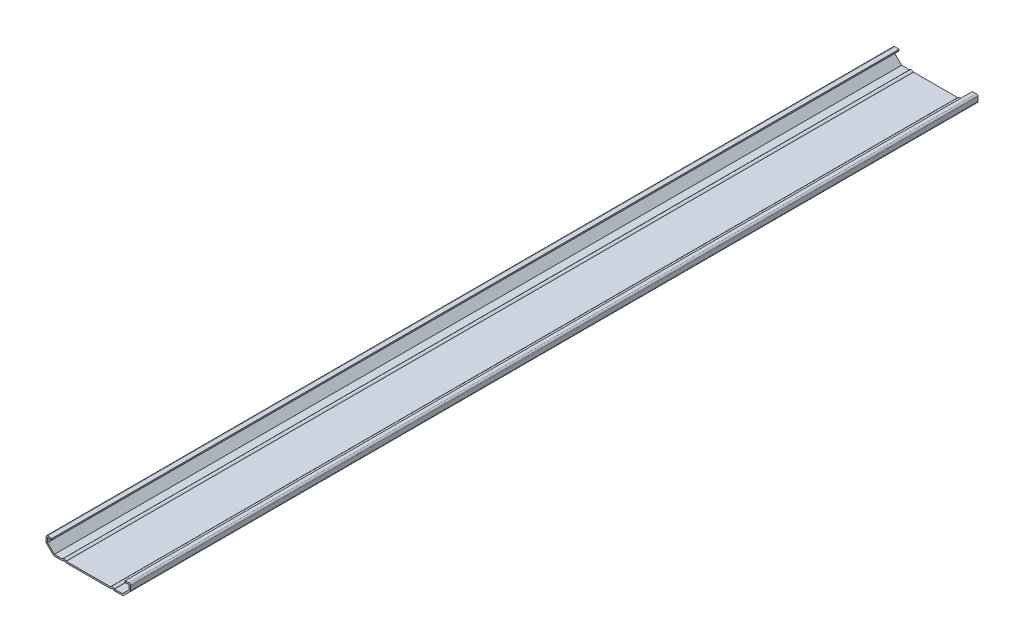
SolidWorks part; units mm, degrees
ref_plane "Front Plane" through (0, 0, 0) normal (0, 0, 1) x (1, 0, 0)
ref_plane "Top Plane" through (0, 0, 0) normal (0, 1, 0) x (1, 0, 0)
ref_plane "Right Plane" through (0, 0, 0) normal (1, 0, 0) x (0, 0, -1)
sketch "Sketch1" plane through (0, 0, 0) normal (0, 0, 1) x (1, 0, 0)
  line L0 (0, 0) -> (0, 6.056) construction
  line L1 (19.05, 0) -> (-19.05, 0)
  line L2 (-20.6375, 0) -> (-28.575, 0)
  line L3 (-28.575, 0) -> (-34.925, 6.35)
  line L4 (-34.925, 6.35) -> (-34.925, 11.9062)
  line L5 (-34.925, 11.9062) -> (-30.1625, 11.5094)
  line L6 (34.925, 11.9062) -> (30.1625, 11.5094)
  line L7 (34.925, 6.35) -> (34.925, 11.9062)
  line L8 (28.575, 0) -> (34.925, 6.35)
  line L9 (20.6375, 0) -> (28.575, 0)
  arc A0 (-19.05, 0) -> (-20.6375, 0) centre (-19.8437, 0) ccw
  arc A1 (19.05, 0) -> (20.6375, 0) centre (19.8437, 0) cw
  point P7 (-15.8425, 0)
  point P11 (-21.9019, 2.9293)
extrude "Extrude-Thin1" add sketch "Sketch1" against normal blind 698.5 thin
fillet "Fillet1" radius 1.27 10 edges at (-19.05, 0, -349.25) (-20.6375, 0, -349.25) (20.6375, 0, -349.25) (19.05, 0, -349.25) (34.925, 11.9062, -349.25) (34.925, 6.35, -349.25) (28.575, 0, -349.25) (-28.575, 0, -349.25) (-34.925, 6.35, -349.25) (-34.925, 11.9062, -349.25)
equation "\"D1@Extrude-Thin1\"=\"D9@Sketch1\"*10"
